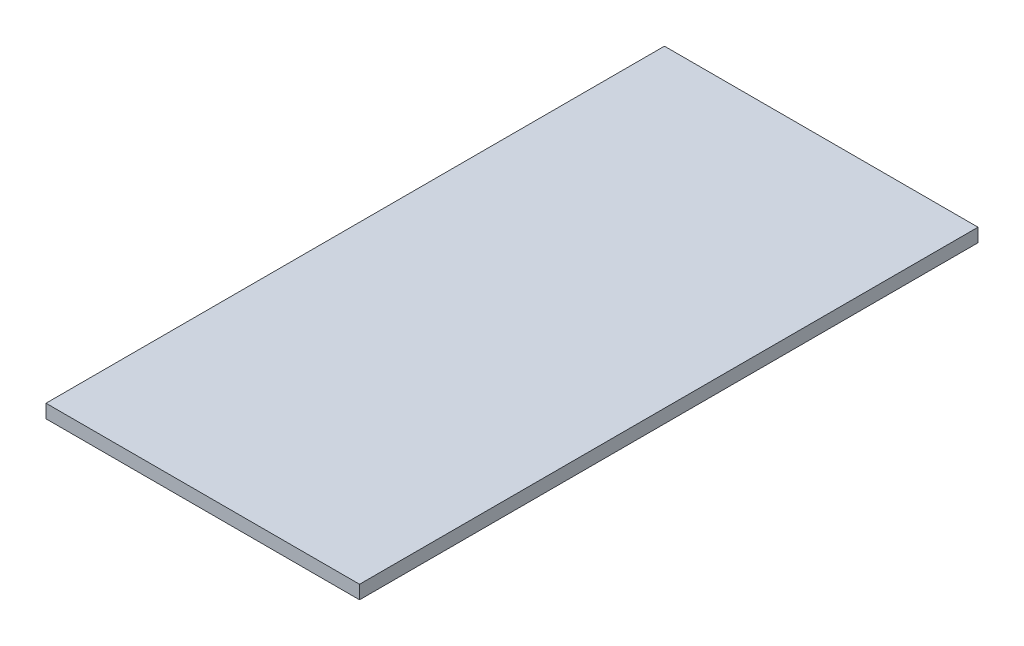
SolidWorks part; units mm, degrees
material "Beech"
ref_plane "Front Plane" through (0, 0, 0) normal (0, 0, 1) x (1, 0, 0)
ref_plane "Top Plane" through (0, 0, 0) normal (0, 1, 0) x (1, 0, 0)
ref_plane "Right Plane" through (0, 0, 0) normal (1, 0, 0) x (0, 0, -1)
other "Configuration Table"
sketch "Sketch2" plane through (0, 0, 0) normal (0, 1, 0) x (1, 0, 0)
  line L1 (-36.83, -72.644) -> (36.83, -72.644)
  line L2 (-36.83, -72.644) -> (-36.83, 72.644)
  line L3 (-36.83, 72.644) -> (36.83, 72.644)
  line L4 (36.83, -72.644) -> (36.83, 72.644)
  line L5 (-36.83, -72.644) -> (36.83, 72.644) construction
  line L6 (-36.83, 72.644) -> (36.83, -72.644) construction
  point P0 (0, 0)
  dimension "D1" = 145.288
  dimension "D2" = 73.66
extrude "Boss-Extrude1" add sketch "Sketch2" along normal blind 3.175
